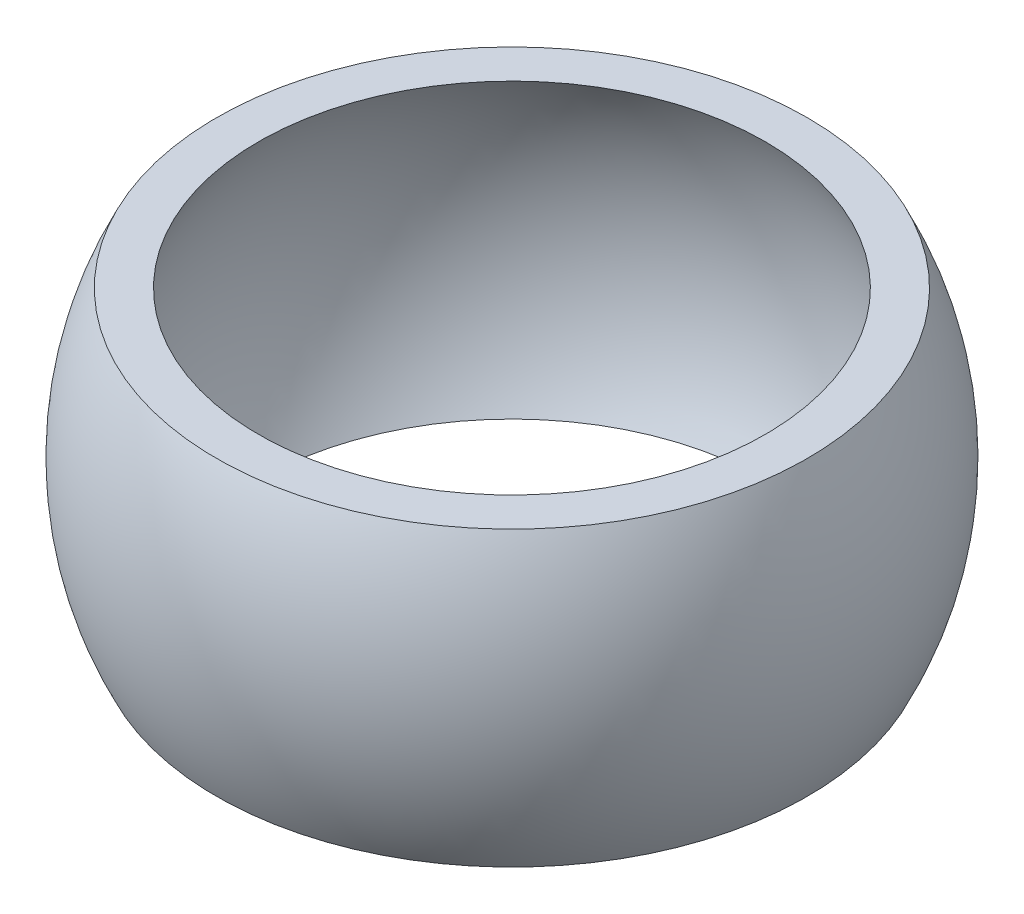
SolidWorks part; units mm, degrees
ref_plane "Front Plane" through (0, 0, 0) normal (0, 0, 1) x (1, 0, 0)
ref_plane "Top Plane" through (0, 0, 0) normal (0, 1, 0) x (1, 0, 0)
ref_plane "Right Plane" through (0, 0, 0) normal (1, 0, 0) x (0, 0, -1)
sketch "Sketch1" plane through (0, 0, 0) normal (0, 0, 1) x (1, 0, 0)
  line L0 (0, 0) -> (0, 28.2585) construction
  line L1 (0, 0) -> (14, 0) construction
  line L2 (12.1244, 7) -> (14.1244, 7)
  line L3 (12.1244, -7) -> (14.1244, -7)
  arc A0 (14, 0) -> (12.1244, 7) centre (0, 0) ccw
  arc A1 (14, 0) -> (12.1244, -7) centre (0, 0) cw
  arc A2 (14.1244, -7) -> (14.1244, 7) centre (0, 0) ccw
  dimension "D3" = 14
  dimension "D1" = 2
  dimension "D2" = 14
revolve "Revolve1" add sketch "Sketch1" angle 360 about L0
